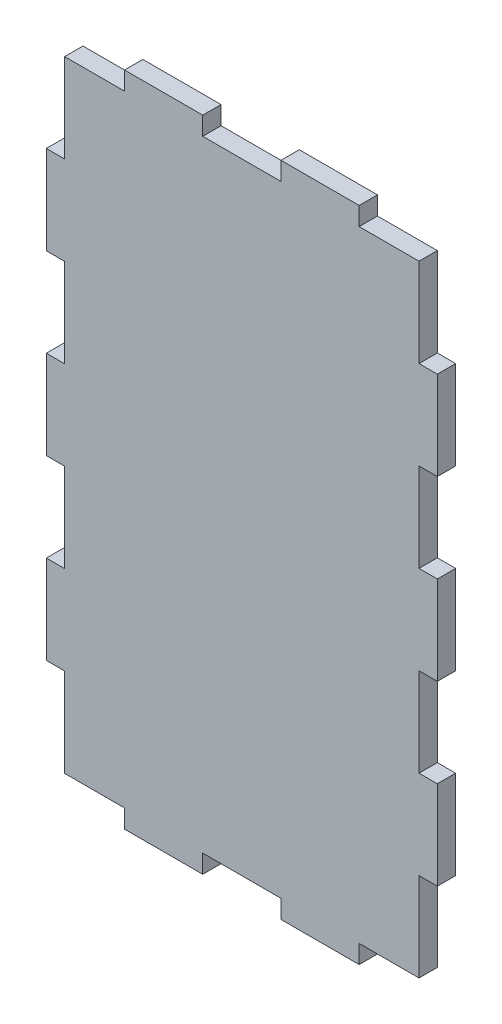
SolidWorks part; units mm, degrees
ref_plane "Alzado" through (0, 0, 0) normal (0, 0, 1) x (1, 0, 0)
ref_plane "Planta" through (0, 0, 0) normal (0, 1, 0) x (1, 0, 0)
ref_plane "Vista lateral" through (0, 0, 0) normal (1, 0, 0) x (0, 0, -1)
sketch "Croquis1" plane through (0, 0, 0) normal (0, 0, 1) x (1, 0, 0)
  line L0 (0, -17.0016) -> (0, -14.0016)
  line L1 (-48.39, -14.0016) -> (0, -14.0016) construction
  line L2 (0, -17.0016) -> (104.61, -17.0016)
  line L3 (101.61, -17.0016) -> (101.61, -49.332) construction
  line L4 (-227.956, -78.0016) -> (93.758, -78.0016) construction
  line L5 (-48.39, -14.0016) -> (-48.39, -78.0016) construction
  line L6 (78.6222, -39.0016) -> (-38.712, -39.0016) construction
  line L7 (0, -14.0016) -> (0, -17.0016) construction
  line L8 (0, -17.0016) -> (-48.39, -17.0016) construction
  line L9 (-48.39, -14.0016) -> (-38.712, -14.0016)
  line L10 (-38.712, -14.0016) -> (-38.712, -17.0016)
  line L11 (-38.712, -17.0016) -> (-29.034, -17.0016)
  line L12 (-29.034, -17.0016) -> (-29.034, -14.0016)
  line L13 (-29.034, -14.0016) -> (-19.356, -14.0016)
  line L14 (-19.356, -14.0016) -> (-19.356, -17.0016)
  line L15 (-19.356, -17.0016) -> (-9.678, -17.0016)
  line L16 (-9.678, -17.0016) -> (-9.678, -14.0016)
  line L17 (-9.678, -14.0016) -> (0, -14.0016)
  line L18 (104.61, -17.0016) -> (104.61, -78.0016) construction
  line L19 (104.61, -17.0016) -> (104.61, -29.2016)
  line L20 (104.61, -29.2016) -> (101.61, -29.2016)
  line L21 (101.61, -29.2016) -> (101.61, -41.4016)
  line L22 (101.61, -41.4016) -> (104.61, -41.4016)
  line L23 (104.61, -41.4016) -> (104.61, -53.6016)
  line L24 (104.61, -53.6016) -> (101.61, -53.6016)
  line L25 (101.61, -53.6016) -> (101.61, -65.8016)
  line L26 (101.61, -65.8016) -> (104.61, -65.8016)
  line L27 (104.61, -65.8016) -> (104.61, -78.0016)
  line L28 (-45.39, -56.5563) -> (-45.39, 45.6638) construction
  line L29 (-48.39, -14.0016) -> (-48.39, -26.8016)
  line L30 (-48.39, -26.8016) -> (-45.39, -26.8016)
  line L31 (-45.39, -26.8016) -> (-45.39, -39.6016)
  line L32 (-45.39, -39.6016) -> (-48.39, -39.6016)
  line L33 (-48.39, -39.6016) -> (-48.39, -52.4016)
  line L34 (-48.39, -52.4016) -> (-45.39, -52.4016)
  line L35 (-45.39, -52.4016) -> (-45.39, -65.2016)
  line L36 (-45.39, -65.2016) -> (-48.39, -65.2016)
  line L37 (-48.39, -65.2016) -> (-48.39, -78.0016)
  line L38 (-102.5031, -75.0016) -> (75.9308, -75.0016) construction
  line L39 (-124.386, -156.1001) -> (179.1879, -156.1001) construction
  line L40 (-48.39, -153.1001) -> (104.61, -153.1001) construction
  line L41 (-48.39, -78.0016) -> (-34.4809, -78.0016)
  line L42 (-34.4809, -78.0016) -> (-34.4809, -75.0016)
  line L43 (-34.4809, -75.0016) -> (-20.5718, -75.0016)
  line L44 (-20.5718, -75.0016) -> (-20.5718, -78.0016)
  line L45 (-20.5718, -78.0016) -> (-6.6627, -78.0016)
  line L46 (-6.6627, -78.0016) -> (-6.6627, -75.0016)
  line L47 (-6.6627, -75.0016) -> (7.2464, -75.0016)
  line L48 (7.2464, -75.0016) -> (7.2464, -78.0016)
  line L49 (7.2464, -78.0016) -> (21.1555, -78.0016)
  line L50 (21.1555, -78.0016) -> (21.1555, -75.0016)
  line L51 (21.1555, -75.0016) -> (35.0645, -75.0016)
  line L52 (35.0645, -75.0016) -> (35.0645, -78.0016)
  line L53 (35.0645, -78.0016) -> (48.9736, -78.0016)
  line L54 (48.9736, -78.0016) -> (48.9736, -75.0016)
  line L55 (48.9736, -75.0016) -> (62.8827, -75.0016)
  line L56 (62.8827, -75.0016) -> (62.8827, -78.0016)
  line L57 (62.8827, -78.0016) -> (76.7918, -78.0016)
  line L58 (76.7918, -78.0016) -> (76.7918, -75.0016)
  line L59 (76.7918, -75.0016) -> (90.7009, -75.0016)
  line L60 (90.7009, -75.0016) -> (90.7009, -78.0016)
  line L61 (90.7009, -78.0016) -> (104.61, -78.0016)
  line L62 (-48.39, -153.1001) -> (-48.39, -260.7101) construction
  line L63 (-48.39, -260.7101) -> (104.61, -260.7101) construction
  line L64 (104.61, -153.1001) -> (104.61, -260.7101) construction
  line L65 (-68.7634, -257.7101) -> (144.8732, -257.7101) construction
  line L66 (101.61, -78.0016) -> (101.61, -269.1968) construction
  line L67 (-45.39, -153.1001) -> (-45.39, -251.8965) construction
  line L68 (-34.4809, -78.0016) -> (-34.4809, -243.0877) construction
  line L69 (-20.5718, -78.0016) -> (-20.5718, -243.0877) construction
  line L70 (-6.6627, -75.0016) -> (-6.6627, -243.0877) construction
  line L71 (7.2464, -75.0016) -> (7.2464, -243.0877) construction
  line L72 (21.1555, -75.0016) -> (21.1555, -243.0877) construction
  line L73 (35.0645, -75.0016) -> (35.0645, -243.0877) construction
  line L74 (48.9736, -75.0016) -> (48.9736, -243.0877) construction
  line L75 (62.8827, -75.0016) -> (62.8827, -243.0877) construction
  line L76 (76.7918, -75.0016) -> (76.7918, -243.0877) construction
  line L77 (90.7009, -75.0016) -> (90.7009, -243.0877) construction
  line L78 (-34.4809, -156.1001) -> (-48.39, -156.1001)
  line L79 (-34.4809, -156.1001) -> (-34.4809, -153.1001)
  line L80 (-34.4809, -153.1001) -> (-20.5718, -153.1001)
  line L81 (-20.5718, -153.1001) -> (-20.5718, -156.1001)
  line L82 (-20.5718, -156.1001) -> (-6.6627, -156.1001)
  line L83 (-6.6627, -156.1001) -> (-6.6627, -153.1001)
  line L84 (-6.6627, -153.1001) -> (7.2464, -153.1001)
  line L85 (7.2464, -153.1001) -> (7.2464, -156.1001)
  line L86 (7.2464, -156.1001) -> (21.1555, -156.1001)
  line L87 (21.1555, -156.1001) -> (21.1555, -153.1001)
  line L88 (21.1555, -153.1001) -> (35.0645, -153.1001)
  line L89 (35.0645, -153.1001) -> (35.0645, -156.1001)
  line L90 (35.0645, -156.1001) -> (48.9736, -156.1001)
  line L91 (48.9736, -156.1001) -> (48.9736, -153.1001)
  line L92 (48.9736, -153.1001) -> (62.8827, -153.1001)
  line L93 (62.8827, -153.1001) -> (62.8827, -156.1001)
  line L94 (62.8827, -156.1001) -> (76.7918, -156.1001)
  line L95 (76.7918, -156.1001) -> (76.7918, -153.1001)
  line L96 (76.7918, -153.1001) -> (90.7009, -153.1001)
  line L97 (90.7009, -153.1001) -> (90.7009, -156.1001)
  line L98 (90.7009, -156.1001) -> (104.61, -156.1001)
  line L99 (-48.39, -257.7101) -> (-34.4809, -257.7101)
  line L100 (-34.4809, -257.7101) -> (-34.4809, -260.7101)
  line L101 (-34.4809, -260.7101) -> (-20.5718, -260.7101)
  line L102 (-20.5718, -260.7101) -> (-20.5718, -257.7101)
  line L103 (-20.5718, -257.7101) -> (-6.6627, -257.7101)
  line L104 (-6.6627, -257.7101) -> (-6.6627, -260.7101)
  line L105 (-6.6627, -260.7101) -> (7.2464, -260.7101)
  line L106 (7.2464, -260.7101) -> (7.2464, -257.7101)
  line L107 (7.2464, -257.7101) -> (21.1555, -257.7101)
  line L108 (21.1555, -257.7101) -> (21.1555, -260.7101)
  line L109 (21.1555, -260.7101) -> (35.0645, -260.7101)
  line L110 (35.0645, -260.7101) -> (35.0645, -257.7101)
  line L111 (35.0645, -257.7101) -> (48.9736, -257.7101)
  line L112 (48.9736, -257.7101) -> (48.9736, -260.7101)
  line L113 (48.9736, -260.7101) -> (62.8827, -260.7101)
  line L114 (62.8827, -260.7101) -> (62.8827, -257.7101)
  line L115 (62.8827, -257.7101) -> (76.7918, -257.7101)
  line L116 (76.7918, -257.7101) -> (76.7918, -260.7101)
  line L117 (76.7918, -260.7101) -> (90.7009, -260.7101)
  line L118 (90.7009, -260.7101) -> (90.7009, -257.7101)
  line L119 (90.7009, -257.7101) -> (104.61, -257.7101)
  line L120 (-224.7521, -14.0016) -> (-224.7521, -78.0016) construction
  line L121 (-288.7521, -78.0016) -> (-224.7521, -78.0016) construction
  line L122 (-224.7521, -78.0016) -> (-224.7521, -287.7111) construction
  line L123 (-288.7521, -78.0016) -> (-288.7521, -287.7111) construction
  line L124 (-288.7521, -287.7111) -> (-224.7521, -287.7111) construction
  line L125 (-48.39, -26.8016) -> (-105.5506, -26.8016) construction
  line L126 (-48.39, -39.6016) -> (-94.7516, -39.6016) construction
  line L127 (-48.39, -52.4016) -> (-71.8061, -52.4016) construction
  line L128 (-48.39, -65.2016) -> (-67.7461, -65.2016) construction
  line L129 (-275.9521, -73.8444) -> (-275.9521, -111.8004) construction
  line L130 (-263.1521, -73.8444) -> (-263.1521, -111.8004) construction
  line L131 (-250.3521, -90.832) -> (-250.3521, -128.788) construction
  line L132 (-237.5521, -73.8444) -> (-237.5521, -111.8004) construction
  line L133 (-227.7521, -73.8444) -> (-227.7521, -93.389) construction
  line L134 (165.3571, -156.1001) -> (174.5571, -156.1001)
  line L135 (174.5571, -156.1001) -> (174.5571, -153.1001)
  line L136 (174.5571, -153.1001) -> (186.7571, -153.1001)
  line L137 (186.7571, -153.1001) -> (186.7571, -156.1001)
  line L138 (186.7571, -156.1001) -> (198.9571, -156.1001)
  line L139 (198.9571, -156.1001) -> (198.9571, -153.1001)
  line L140 (198.9571, -153.1001) -> (211.1571, -153.1001)
  line L141 (211.1571, -153.1001) -> (211.1571, -156.1001)
  line L142 (211.1571, -156.1001) -> (223.3571, -156.1001)
  line L143 (-227.7521, -156.1001) -> (-227.7521, -170.6158)
  line L144 (-227.7521, -170.6158) -> (-224.7521, -170.6158)
  line L145 (-224.7521, -170.6158) -> (-224.7521, -185.1315)
  line L146 (-224.7521, -185.1315) -> (-227.7521, -185.1315)
  line L147 (-227.7521, -185.1315) -> (-227.7521, -199.6473)
  line L148 (-227.7521, -199.6473) -> (-224.7521, -199.6473)
  line L149 (-224.7521, -199.6473) -> (-224.7521, -214.163)
  line L150 (-224.7521, -214.163) -> (-227.7521, -214.163)
  line L151 (-48.39, -257.7101) -> (-48.39, -243.1944)
  line L152 (-48.39, -243.1944) -> (-45.39, -243.1944)
  line L153 (-45.39, -243.1944) -> (-45.39, -228.6787)
  line L154 (-45.39, -228.6787) -> (-48.39, -228.6787)
  line L155 (-48.39, -228.6787) -> (-48.39, -214.163)
  line L156 (-48.39, -214.163) -> (-45.39, -214.163)
  line L157 (-45.39, -214.163) -> (-45.39, -199.6473)
  line L158 (-45.39, -199.6473) -> (-48.39, -199.6473)
  line L159 (-48.39, -199.6473) -> (-48.39, -185.1315)
  line L160 (-48.39, -185.1315) -> (-45.39, -185.1315)
  line L161 (-45.39, -185.1315) -> (-45.39, -170.6158)
  line L162 (-45.39, -170.6158) -> (-48.39, -170.6158)
  line L163 (-48.39, -170.6158) -> (-48.39, -156.1001)
  line L164 (-48.39, -228.6787) -> (-80.3979, -228.6787) construction
  line L165 (-48.39, -243.1944) -> (-76.899, -243.1944) construction
  line L166 (-48.39, -214.163) -> (-74.7996, -214.163) construction
  line L167 (-48.39, -199.6473) -> (-74.7996, -199.6473) construction
  line L168 (-74.7996, -185.1315) -> (-48.39, -185.1315) construction
  line L169 (-48.39, -170.6158) -> (-71.0675, -170.6158) construction
  line L170 (-227.7521, -214.163) -> (-227.7521, -228.6787)
  line L171 (-285.7521, -73.8444) -> (-285.7521, -109.848) construction
  line L172 (-227.7521, -228.6787) -> (-224.7521, -228.6787)
  line L173 (-224.7521, -228.6787) -> (-224.7521, -243.1944)
  line L174 (-224.7521, -243.1944) -> (-227.7521, -243.1944)
  line L175 (-227.7521, -243.1944) -> (-227.7521, -257.7101)
  line L176 (223.3571, -257.7101) -> (211.1571, -257.7101)
  line L177 (211.1571, -257.7101) -> (211.1571, -260.7101)
  line L178 (211.1571, -260.7101) -> (198.9571, -260.7101)
  line L179 (198.9571, -260.7101) -> (198.9571, -257.7101)
  line L180 (198.9571, -257.7101) -> (186.7571, -257.7101)
  line L181 (186.7571, -257.7101) -> (186.7571, -260.7101)
  line L182 (186.7571, -260.7101) -> (174.5571, -260.7101)
  line L183 (174.5571, -260.7101) -> (174.5571, -257.7101)
  line L184 (-285.7521, -257.7101) -> (-285.7521, -243.1944)
  line L185 (-285.7521, -243.1944) -> (-288.7521, -243.1944)
  line L186 (-288.7521, -243.1944) -> (-288.7521, -228.6787)
  line L187 (-288.7521, -228.6787) -> (-285.7521, -228.6787)
  line L188 (-285.7521, -228.6787) -> (-285.7521, -214.163)
  line L189 (-285.7521, -214.163) -> (-288.7521, -214.163)
  line L190 (-288.7521, -214.163) -> (-288.7521, -199.6473)
  line L191 (-288.7521, -199.6473) -> (-285.7521, -199.6473)
  line L192 (-285.7521, -199.6473) -> (-285.7521, -185.1315)
  line L193 (-285.7521, -185.1315) -> (-288.7521, -185.1315)
  line L194 (-288.7521, -185.1315) -> (-288.7521, -170.6158)
  line L195 (-288.7521, -170.6158) -> (-285.7521, -170.6158)
  line L196 (-285.7521, -170.6158) -> (-285.7521, -156.1001)
  line L197 (174.5571, -257.7101) -> (165.3571, -257.7101)
  line L198 (-315.487, -120.5373) -> (-315.487, -274.6014) construction
  line L199 (-423.097, -153.1001) -> (-423.097, -80.2802) construction
  line L200 (-420.097, -153.1001) -> (-420.097, -73.0846) construction
  line L201 (-405.5813, -153.1001) -> (-405.5813, -73.0846) construction
  line L202 (-391.0655, -153.1001) -> (-391.0655, -77.6291) construction
  line L203 (-376.5498, -153.1001) -> (-376.5498, -80.2802) construction
  line L204 (-362.0341, -153.1001) -> (-362.0341, -73.0846) construction
  line L205 (-347.5184, -153.1001) -> (-347.5184, -77.6291) construction
  line L206 (-333.0027, -153.1001) -> (-333.0027, -73.0846) construction
  line L207 (-318.487, -153.1001) -> (-318.487, -77.6291) construction
  line L208 (-48.39, -21.6772) -> (-48.39, 38.9813) construction
  line L209 (-38.712, -14.0016) -> (-38.712, 45.6638) construction
  line L210 (-29.034, -14.0016) -> (-29.034, 45.6638) construction
  line L211 (-19.356, -14.0016) -> (-19.356, 45.6638) construction
  line L212 (-9.678, -14.0016) -> (-9.678, 45.6638) construction
  line L213 (0, -14.0016) -> (0, 45.6638) construction
  line L214 (2.5149, 38.1832) -> (-48.39, 38.1832) construction
  line L215 (-48.39, 86.5732) -> (-80.1148, 86.5732) construction
  line L216 (-48.39, 76.8952) -> (-75.2531, 76.8952) construction
  line L217 (-48.39, 67.2172) -> (-75.2531, 67.2172) construction
  line L218 (-48.39, 57.5392) -> (-80.1148, 57.5392) construction
  line L219 (-48.39, 47.8612) -> (-84.9766, 47.8612) construction
  line L220 (-318.487, 38.1832) -> (-318.487, 47.8612)
  line L221 (-48.39, 38.1832) -> (-76.9441, 38.1832) construction
  line L222 (-318.487, 47.8612) -> (-315.487, 47.8612)
  line L223 (-315.487, 47.8612) -> (-315.487, 57.5392)
  line L224 (-315.487, 57.5392) -> (-318.487, 57.5392)
  line L225 (-318.487, 57.5392) -> (-318.487, 67.2172)
  line L226 (-318.487, 67.2172) -> (-315.487, 67.2172)
  line L227 (-315.487, 67.2172) -> (-315.487, 76.8952)
  line L228 (-315.487, 76.8952) -> (-318.487, 76.8952)
  line L229 (-318.487, 76.8952) -> (-318.487, 86.5732)
  line L230 (-318.487, 86.5732) -> (-420.097, 86.5732)
  line L231 (-420.097, 86.5732) -> (-420.097, 76.8952)
  line L232 (-420.097, 76.8952) -> (-423.097, 76.8952)
  line L233 (-423.097, 76.8952) -> (-423.097, 67.2172)
  line L234 (-423.097, 67.2172) -> (-420.097, 67.2172)
  line L235 (-420.097, 67.2172) -> (-420.097, 57.5392)
  line L236 (-420.097, 57.5392) -> (-423.097, 57.5392)
  line L237 (-423.097, 57.5392) -> (-423.097, 47.8612)
  line L238 (-423.097, 47.8612) -> (-420.097, 47.8612)
  line L239 (-420.097, 47.8612) -> (-420.097, 38.1832)
  line L240 (-48.39, 41.1832) -> (-83.9517, 41.1832) construction
  line L241 (-318.487, 38.1832) -> (-333.0027, 38.1832)
  line L242 (-333.0027, 38.1832) -> (-333.0027, 41.1832)
  line L243 (-333.0027, 41.1832) -> (-347.5184, 41.1832)
  line L244 (-347.5184, 41.1832) -> (-347.5184, 38.1832)
  line L245 (-347.5184, 38.1832) -> (-362.0341, 38.1832)
  line L246 (-362.0341, 38.1832) -> (-362.0341, 41.1832)
  line L247 (-362.0341, 41.1832) -> (-376.5498, 41.1832)
  line L248 (-376.5498, 41.1832) -> (-376.5498, 38.1832)
  line L249 (-376.5498, 38.1832) -> (-391.0655, 38.1832)
  line L250 (-391.0655, 38.1832) -> (-391.0655, 41.1832)
  line L251 (-391.0655, 41.1832) -> (-405.5813, 41.1832)
  line L252 (-405.5813, 41.1832) -> (-405.5813, 38.1832)
  line L253 (-405.5813, 38.1832) -> (-420.097, 38.1832)
  line L254 (162.3571, -15.1529) -> (162.3571, -104.9762) construction
  line L255 (104.61, -29.2016) -> (145.8916, -29.2016) construction
  line L256 (104.61, -41.4016) -> (145.8916, -41.4016) construction
  line L257 (104.61, -65.8016) -> (131.4417, -65.8016) construction
  line L258 (104.61, -53.6016) -> (126.5441, -53.6016) construction
  line L259 (165.3571, -73.8444) -> (165.3571, -106.8492) construction
  line L260 (174.5571, -73.8444) -> (174.5571, -108.8044) construction
  line L261 (186.7571, -73.8444) -> (186.7571, -108.8044) construction
  line L262 (198.9571, -73.8444) -> (198.9571, -108.8044) construction
  line L263 (211.1571, -73.8444) -> (211.1571, -106.8492) construction
  line L264 (223.3571, -73.8444) -> (223.3571, -108.8044) construction
  line L265 (104.61, -257.7101) -> (104.61, -243.0877)
  line L266 (104.61, -243.0877) -> (101.61, -243.0877)
  line L267 (101.61, -243.0877) -> (101.61, -228.6787)
  line L268 (101.61, -228.6787) -> (104.61, -228.6787)
  line L269 (104.61, -228.6787) -> (104.61, -214.163)
  line L270 (104.61, -214.163) -> (101.61, -214.163)
  line L271 (101.61, -214.163) -> (101.61, -199.6473)
  line L272 (101.61, -199.6473) -> (104.61, -199.6473)
  line L273 (104.61, -199.6473) -> (104.61, -185.1315)
  line L274 (104.61, -185.1315) -> (101.61, -185.1315)
  line L275 (101.61, -185.1315) -> (101.61, -170.6158)
  line L276 (101.61, -170.6158) -> (104.61, -170.6158)
  line L277 (104.61, -170.6158) -> (104.61, -156.1001)
  line L278 (-227.7521, -156.1001) -> (-237.5521, -156.1001)
  line L279 (-237.5521, -156.1001) -> (-237.5521, -153.1001)
  line L280 (-237.5521, -153.1001) -> (-250.3521, -153.1001)
  line L281 (-250.3521, -153.1001) -> (-250.3521, -156.1001)
  line L282 (-250.3521, -156.1001) -> (-263.1521, -156.1001)
  line L283 (-263.1521, -156.1001) -> (-263.1521, -153.1001)
  line L284 (-263.1521, -153.1001) -> (-275.9521, -153.1001)
  line L285 (-275.9521, -153.1001) -> (-275.9521, -156.1001)
  line L286 (-275.9521, -156.1001) -> (-285.7521, -156.1001)
  line L287 (223.3571, -156.1001) -> (223.3571, -257.7101)
  line L288 (-227.7521, -257.7101) -> (-237.5521, -257.7101)
  line L289 (-237.5521, -257.7101) -> (-237.5521, -260.7101)
  line L290 (-237.5521, -260.7101) -> (-250.3521, -260.7101)
  line L291 (-250.3521, -260.7101) -> (-250.3521, -257.7101)
  line L292 (-250.3521, -257.7101) -> (-263.1521, -257.7101)
  line L293 (-263.1521, -257.7101) -> (-263.1521, -260.7101)
  line L294 (-263.1521, -260.7101) -> (-275.9521, -260.7101)
  line L295 (-275.9521, -260.7101) -> (-275.9521, -257.7101)
  line L296 (-275.9521, -257.7101) -> (-285.7521, -257.7101)
  line L297 (165.3571, -257.7101) -> (165.3571, -243.1944)
  line L298 (165.3571, -243.1944) -> (162.3571, -243.1944)
  line L299 (162.3571, -243.1944) -> (162.3571, -228.6787)
  line L300 (162.3571, -228.6787) -> (165.3571, -228.6787)
  line L301 (165.3571, -228.6787) -> (165.3571, -214.163)
  line L302 (165.3571, -214.163) -> (162.3571, -214.163)
  line L303 (162.3571, -214.163) -> (162.3571, -199.6473)
  line L304 (162.3571, -199.6473) -> (165.3571, -199.6473)
  line L305 (165.3571, -199.6473) -> (165.3571, -185.1315)
  line L306 (165.3571, -185.1315) -> (162.3571, -185.1315)
  line L307 (162.3571, -185.1315) -> (162.3571, -170.6158)
  line L308 (162.3571, -170.6158) -> (165.3571, -170.6158)
  line L309 (165.3571, -170.6158) -> (165.3571, -156.1001)
  circle A0 centre (73.11, -39.0016) radius 1.25
  circle A1 centre (31.5, -39.0016) radius 1.25
  circle A2 centre (-28.49, -39.0016) radius 1.25
  arc A3 (-224.7521, -65.2016) -> (-237.5521, -78.0016) centre (-224.7521, -78.0016) ccw construction
  arc A4 (-224.7521, -52.4016) -> (-250.3521, -78.0016) centre (-224.7521, -78.0016) ccw construction
  arc A5 (-224.7521, -39.6016) -> (-263.1521, -78.0016) centre (-224.7521, -78.0016) ccw construction
  arc A6 (-224.7521, -26.8016) -> (-275.9521, -78.0016) centre (-224.7521, -78.0016) ccw construction
  arc A7 (-224.7521, -14.0016) -> (-288.7521, -78.0016) centre (-224.7521, -78.0016) ccw construction
  arc A8 (-224.7521, -75.0016) -> (-227.7521, -78.0016) centre (-224.7521, -78.0016) ccw construction
  arc A9 (-224.7521, -17.0016) -> (-285.7521, -78.0016) centre (-224.7521, -78.0016) ccw construction
  arc A10 (-315.487, -156.1001) -> (-318.487, -153.1001) centre (-315.487, -153.1001) cw construction
  arc A11 (-315.487, -170.6158) -> (-333.0027, -153.1001) centre (-315.487, -153.1001) cw construction
  arc A12 (-315.487, -185.1315) -> (-347.5184, -153.1001) centre (-315.487, -153.1001) cw construction
  arc A13 (-315.487, -199.6473) -> (-362.0341, -153.1001) centre (-315.487, -153.1001) cw construction
  arc A14 (-315.487, -214.163) -> (-376.5498, -153.1001) centre (-315.487, -153.1001) cw construction
  arc A15 (-315.487, -228.6787) -> (-391.0655, -153.1001) centre (-315.487, -153.1001) cw construction
  arc A16 (-315.487, -243.1944) -> (-405.5813, -153.1001) centre (-315.487, -153.1001) cw construction
  arc A17 (-315.487, -257.7101) -> (-420.097, -153.1001) centre (-315.487, -153.1001) cw construction
  arc A18 (-315.487, -260.7101) -> (-423.097, -153.1001) centre (-315.487, -153.1001) cw construction
  arc A19 (-45.39, 38.1832) -> (-48.39, 41.1832) centre (-48.39, 38.1832) ccw construction
  arc A20 (-38.712, 38.1832) -> (-48.39, 47.8612) centre (-48.39, 38.1832) ccw construction
  arc A21 (-29.034, 38.1832) -> (-48.39, 57.5392) centre (-48.39, 38.1832) ccw construction
  arc A22 (-19.356, 38.1832) -> (-48.39, 67.2172) centre (-48.39, 38.1832) ccw construction
  arc A23 (-9.678, 38.1832) -> (-48.39, 76.8952) centre (-48.39, 38.1832) ccw construction
  arc A24 (0, 38.1832) -> (-48.39, 86.5732) centre (-48.39, 38.1832) ccw construction
  arc A25 (162.3571, -75.0016) -> (165.3571, -78.0016) centre (162.3571, -78.0016) cw construction
  arc A26 (162.3571, -65.8016) -> (174.5571, -78.0016) centre (162.3571, -78.0016) cw construction
  arc A27 (162.3571, -53.6016) -> (186.7571, -78.0016) centre (162.3571, -78.0016) cw construction
  arc A28 (162.3571, -41.4016) -> (198.9571, -78.0016) centre (162.3571, -78.0016) cw construction
  arc A29 (162.3571, -29.2016) -> (211.1571, -78.0016) centre (162.3571, -78.0016) cw construction
  arc A30 (162.3571, -17.0016) -> (223.3571, -78.0016) centre (162.3571, -78.0016) cw construction
  text T0 "TOP\r\n"
  dimension "D2" = 2.5
  dimension "D3" = 2.5
  dimension "D4" = 2.5
  dimension "D7" = 101.6
  dimension "D20" = 22
  dimension "D9" = 36
  dimension "D1" = 153
  dimension "D5" = 3
  dimension "D6" = 104.61
  dimension "D8" = 3
  dimension "D10" = 3
  dimension "D11" = 41.61
  dimension "D13" = 3
  dimension "D14" = 153
  dimension "D15" = 107.61
  dimension "D17" = 3
  dimension "D18" = 3
  dimension "D19" = 28.5
extrude "Saliente-Extruir1" add sketch "Croquis1" along normal blind 3 contours L296 L295 L294 L293 L292 L291 L290 L289 L288 L175 L174 L173 L172 L170 L150 L149 L148 L147 L146 L145 L144 L143 L278 L279 L280 L281 L282 L283 L284 L285 L286 L196 L195 L194 L193 L192 L191 L190 L189 L188 L187 L186 L185 L184
